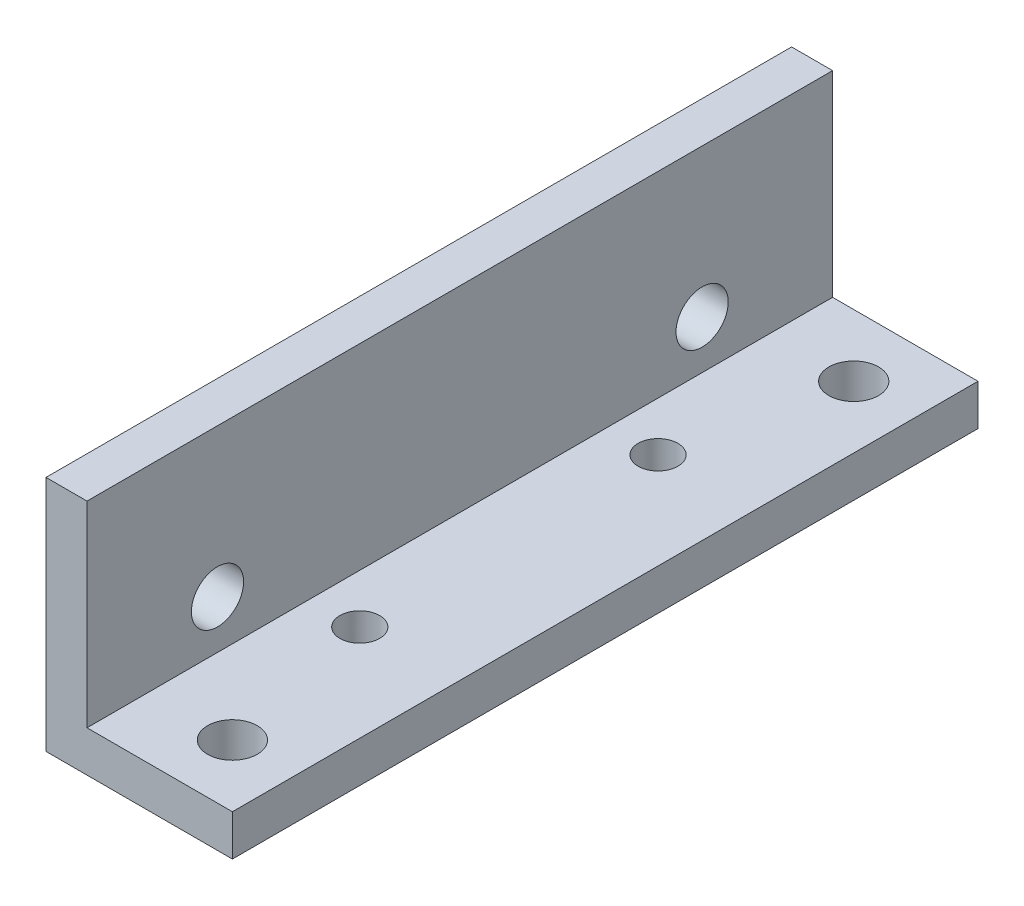
SolidWorks part; units mm, degrees
ref_plane "Front Plane" through (0, 0, 0) normal (0, 0, 1) x (1, 0, 0)
ref_plane "Top Plane" through (0, 0, 0) normal (0, 1, 0) x (1, 0, 0)
ref_plane "Right Plane" through (0, 0, 0) normal (1, 0, 0) x (0, 0, -1)
sketch "Sketch1" plane through (0, 0, 0) normal (0, 0, 1) x (1, 0, 0)
  line L0 (0, 0) -> (0, 19.1)
  line L1 (0, 19.1) -> (3.3, 19.1)
  line L2 (3.3, 19.1) -> (3.3, 3.3)
  line L3 (3.3, 3.3) -> (19.1, 3.3)
  line L4 (19.1, 3.3) -> (19.1, 0)
  line L5 (19.1, 0) -> (0, 0)
  dimension "D1" = 19.1
  dimension "D2" = 19.1
  dimension "D3" = 3.3
  dimension "D4" = 3.3
extrude "Extrude1" add sketch "Sketch1" along normal mid plane 60
sketch "Sketch2" plane through (0, 0, 0) normal (0, -1, 0) x (1, 0, 0)
  line L0 (0, -30) -> (19.1, -30) construction
  line L1 (19.1, 30) -> (15, 30)
  line L2 (19.1, 30) -> (19.1, -30)
  line L3 (19.1, -30) -> (15, -30)
  line L4 (15, 30) -> (15, -30)
  line L5 (0, 30) -> (0, -30) construction
  dimension "D1" = 15
extrude "Cut for walker chassis" cut sketch "Sketch2" against normal through all
hole_wizard "Ø4.2 (4.2) Diameter Hole1" positions "Sketch4" profile "Sketch3" hole size "Ø4.2" standard "Ansi Metric" end condition through all
sketch "Sketch4" plane through (0, 0, 0) normal (-1, 0, 0) x (0, 0, 1)
  line L0 (30, 0) -> (-30, 0) construction
  point P0 (-19.5, 7.18)
  point P1 (19.5, 7.18)
  dimension "D1" = 39
  dimension "D2" = 19.5
  dimension "D3" = 7.18
sketch "Sketch3" plane through (0, 7.18, -19.5) normal (0, 1, 0) x (0, 0, 1)
  line L0 (0, 0) -> (0, 15)
  line L1 (0, 15) -> (2.1, 15)
  line L2 (2.1, 15) -> (2.1, 0)
  line L5 (2.1, 0) -> (0, 0)
  line L11 (0, -6.35) -> (0, 107.95) construction
  dimension "Thru Hole Dia." = 4.2
  dimension "Thru Hole Depth" = 15
hole_wizard "M4x0.7 Tapped Hole1" positions "Sketch6" profile "Sketch5" tap size "M4x0.7" standard "Ansi Metric" end condition up to next
sketch "Sketch6" plane through (0, 0, 0) normal (0, -1, 0) x (1, 0, 0)
  line L0 (0, -30) -> (15, -30) construction
  line L1 (0, 30) -> (15, 30) construction
  line L2 (15, 30) -> (15, -30) construction
  point P0 (10, 25)
  point P1 (10, -25)
  dimension "D1" = 5
  dimension "D2" = 5
  dimension "D3" = 5
sketch "Sketch5" plane through (10, 0, 25) normal (1, 0, 0) x (0, 0, -1)
  line L0 (0, 0) -> (0, 3.3)
  line L1 (0, 3.3) -> (2, 3.3)
  line L2 (2, 3.3) -> (2, 0)
  line L5 (2, 0) -> (0, 0)
  line L11 (0, -6.35) -> (0, 107.95) construction
  dimension "Thread Major Dia." = 4
  dimension "Thru Tap Drill Depth" = 3.3
sketch "Sketch7" plane through (0, 0, 0) normal (0, -1, 0) x (1, 0, 0)
  line L0 (-4.1016, 0) -> (20.1367, 0) construction
  line L1 (0, 30) -> (0, -30) construction
  circle A2 centre (7.25, -12) radius 1.6
  circle A3 centre (7.25, 12) radius 1.6
  dimension "D1" = 3.2
  dimension "D2" = 12
  dimension "D3" = 24
  dimension "D4" = 7.25
extrude "Cut-Extrude1" cut sketch "Sketch7" against normal through all
